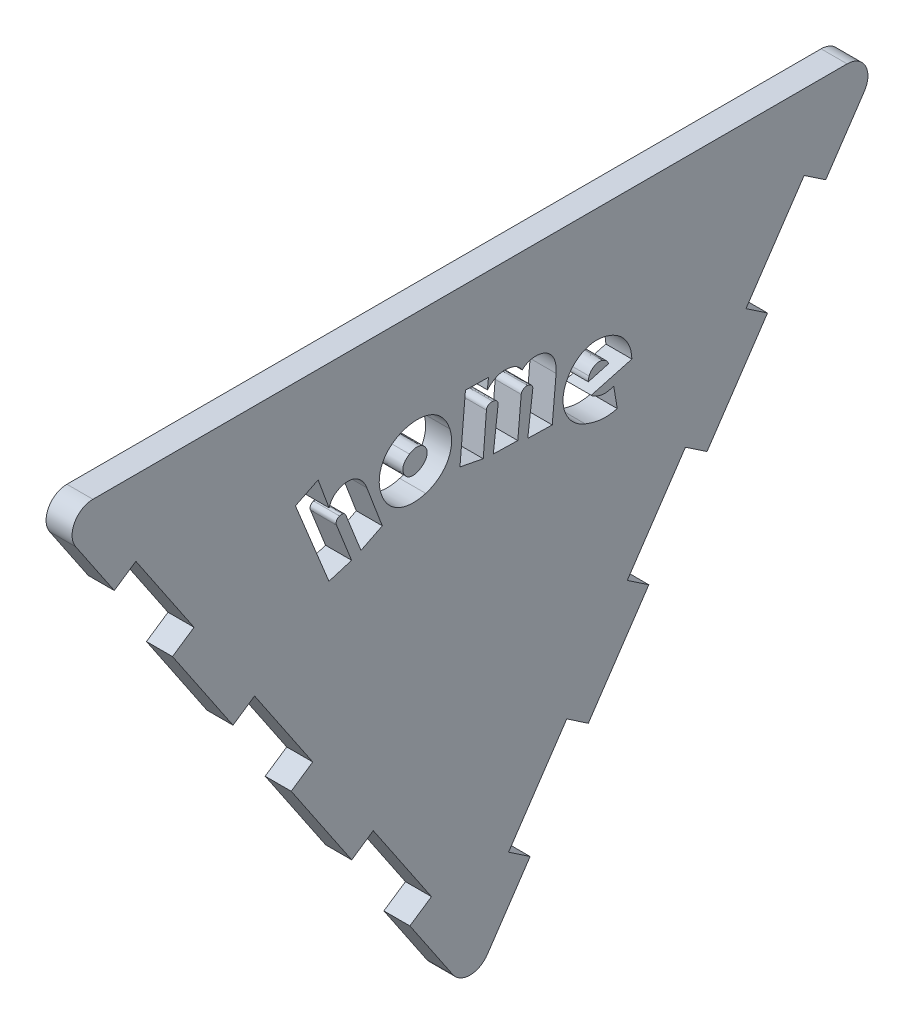
SolidWorks part; units mm, degrees
ref_plane "Front Plane" through (0, 0, 0) normal (0, 0, 1) x (1, 0, 0)
ref_plane "Top Plane" through (0, 0, 0) normal (0, 1, 0) x (1, 0, 0)
ref_plane "Right Plane" through (0, 0, 0) normal (1, 0, 0) x (0, 0, -1)
sketch "Sketch1" plane through (0, 0, 0) normal (1, 0, 0) x (0, 0, -1)
  line L0 (-2.1058, 3.1219) -> (-48.1287, 71.3537)
  line L1 (-46.023, 75.3141) -> (46.023, 75.3141)
  line L2 (48.1287, 71.3537) -> (2.1058, 3.1219)
  line L3 (0, 0) -> (0, 66.7728) construction
  arc A0 (-48.1287, 71.3537) -> (-46.023, 75.3141) centre (-46.023, 72.7741) cw
  arc A1 (46.023, 75.3141) -> (48.1287, 71.3537) centre (46.023, 72.7741) cw
  arc A2 (-2.1058, 3.1219) -> (2.1058, 3.1219) centre (0, 4.5423) ccw
  point P7 (-50.8, 75.3141)
  point P10 (50.8, 75.3141)
  dimension "D4" = 2.54
  dimension "D1" = 101.6
  dimension "D2" = 34
  dimension "D3" = 34
extrude "Extrude1" add sketch "Sketch1" along normal blind 3.175
sketch "Sketch2" plane through (3.175, 0, 0) normal (1, 0, 0) x (0, 0, -1)
  line L0 (-43.4142, 64.3642) -> (-40.782, 66.1396)
  line L1 (-48.1287, 71.3537) -> (-2.1058, 3.1219) construction
  line L2 (-40.782, 66.1396) -> (-33.6802, 55.6108)
  line L3 (-33.6802, 55.6108) -> (-36.3124, 53.8354)
  line L4 (-43.4142, 64.3642) -> (-36.3124, 53.8354)
  line L5 (-50.8, 75.3141) -> (0, 0) construction
  line L6 (-28.9266, 42.8855) -> (-21.8249, 32.3567)
  line L7 (-26.2944, 44.6609) -> (-19.1927, 34.1321)
  line L8 (-19.1927, 34.1321) -> (-21.8249, 32.3567)
  line L9 (-28.9266, 42.8855) -> (-26.2944, 44.6609)
  line L10 (-11.8068, 23.1822) -> (-4.7051, 12.6534)
  line L11 (-14.439, 21.4068) -> (-7.3373, 10.878)
  line L12 (-14.439, 21.4068) -> (-11.8068, 23.1822)
  line L13 (-4.7051, 12.6534) -> (-7.3373, 10.878)
  line L14 (0, 0) -> (0, 90.7535) construction
  line L15 (4.7051, 12.6534) -> (7.3373, 10.878)
  line L16 (14.439, 21.4068) -> (11.8068, 23.1822)
  line L17 (14.439, 21.4068) -> (7.3373, 10.878)
  line L18 (11.8068, 23.1822) -> (4.7051, 12.6534)
  line L19 (28.9266, 42.8855) -> (26.2944, 44.6609)
  line L20 (19.1927, 34.1321) -> (21.8249, 32.3567)
  line L21 (26.2944, 44.6609) -> (19.1927, 34.1321)
  line L22 (28.9266, 42.8855) -> (21.8249, 32.3567)
  line L23 (43.4142, 64.3642) -> (36.3124, 53.8354)
  line L24 (33.6802, 55.6108) -> (36.3124, 53.8354)
  line L25 (40.782, 66.1396) -> (33.6802, 55.6108)
  line L26 (43.4142, 64.3642) -> (40.782, 66.1396)
  line L27 (-50.8, 75.3141) -> (0, 0) construction
  dimension "D1" = 12.7
  dimension "D2" = 3.175
  dimension "D3" = 13.208
  dimension "D5" = 13.208
  dimension "D6" = 13.208
extrude "Cut-Extrude1" cut sketch "Sketch2" against normal through all
sketch "Sketch3" plane through (3.175, 0, 0) normal (1, 0, 0) x (0, 0, -1)
  arc A0 (-28.9266, 42.8855) -> (28.9266, 42.8855) centre (0, 18.4) cw construction
  text T0 "home" font "GROBOLD" height in points 45
extrude "Cut-Extrude2" cut sketch "Sketch3" against normal through all
